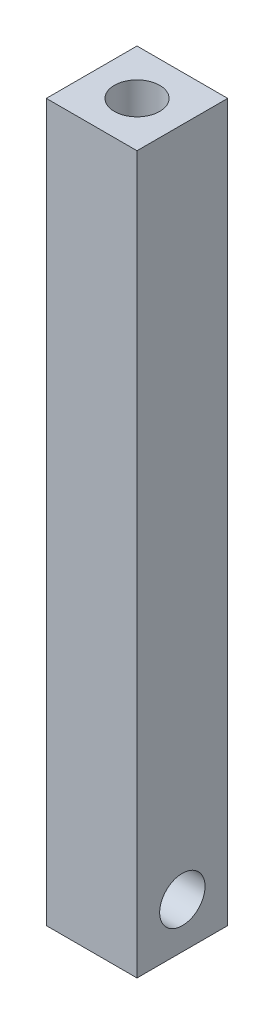
SolidWorks part; units mm, degrees
ref_plane "Front Plane" through (0, 0, 0) normal (0, 0, 1) x (1, 0, 0)
ref_plane "Top Plane" through (0, 0, 0) normal (0, 1, 0) x (1, 0, 0)
ref_plane "Right Plane" through (0, 0, 0) normal (1, 0, 0) x (0, 0, -1)
sketch "Sketch2" plane through (0, 0, 0) normal (1, 0, 0) x (0, 0, -1)
  line L1 (-5, -39.5) -> (5, -39.5)
  line L2 (-5, -39.5) -> (-5, 39.5)
  line L3 (-5, 39.5) -> (5, 39.5)
  line L4 (5, -39.5) -> (5, 39.5)
  line L5 (-5, -39.5) -> (5, 39.5) construction
  line L6 (-5, 39.5) -> (5, -39.5) construction
  circle A0 centre (0, -34.5) radius 2.5
  point P0 (0, 0)
  dimension "D4" = 5
  dimension "D1" = 79
  dimension "D2" = 10
  dimension "D3" = 5
extrude "Boss-Extrude1" add sketch "Sketch2" along normal blind 10
sketch "Sketch3" plane through (0, 39.5, 0) normal (0, 1, 0) x (1, 0, 0)
  line L0 (10, 5) -> (10, -5) construction
  circle A0 centre (5, 0) radius 2.5
  dimension "D2" = 5
  dimension "D1" = 5
extrude "Cut-Extrude1" cut sketch "Sketch3" against normal blind 5
